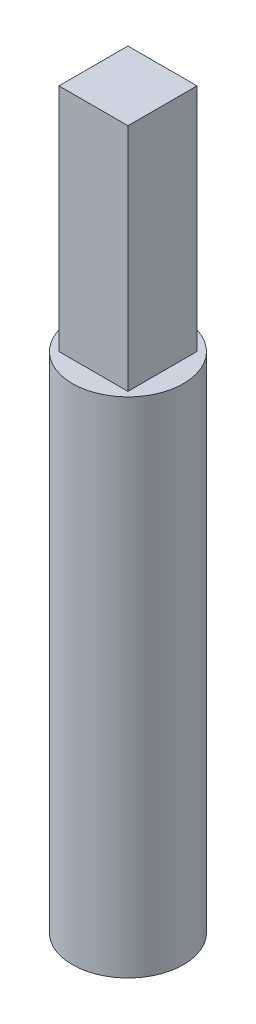
SolidWorks part; units mm, degrees
ref_plane "Front Plane" through (0, 0, 0) normal (0, 0, 1) x (1, 0, 0)
ref_plane "Top Plane" through (0, 0, 0) normal (0, 1, 0) x (1, 0, 0)
ref_plane "Right Plane" through (0, 0, 0) normal (1, 0, 0) x (0, 0, -1)
sketch "Sketch1" plane through (0, 0, 0) normal (0, 1, 0) x (1, 0, 0)
  circle A0 centre (0, 0) radius 3.6805
extrude "Boss-Extrude1" add sketch "Sketch1" along normal blind 33.3375
sketch "Sketch2" plane through (0, 33.3375, 0) normal (0, 1, 0) x (1, 0, 0)
  line L1 (-2.286, 2.286) -> (2.286, 2.286)
  line L2 (-2.286, 2.286) -> (-2.286, -2.286)
  line L3 (-2.286, -2.286) -> (2.286, -2.286)
  line L4 (2.286, 2.286) -> (2.286, -2.286)
  line L5 (-2.286, 2.286) -> (2.286, -2.286) construction
  line L6 (-2.286, -2.286) -> (2.286, 2.286) construction
  point P0 (0, 0)
  dimension "D1" = 4.572
  dimension "D2" = 4.572
extrude "Boss-Extrude2" add sketch "Sketch2" along normal blind 15.24
